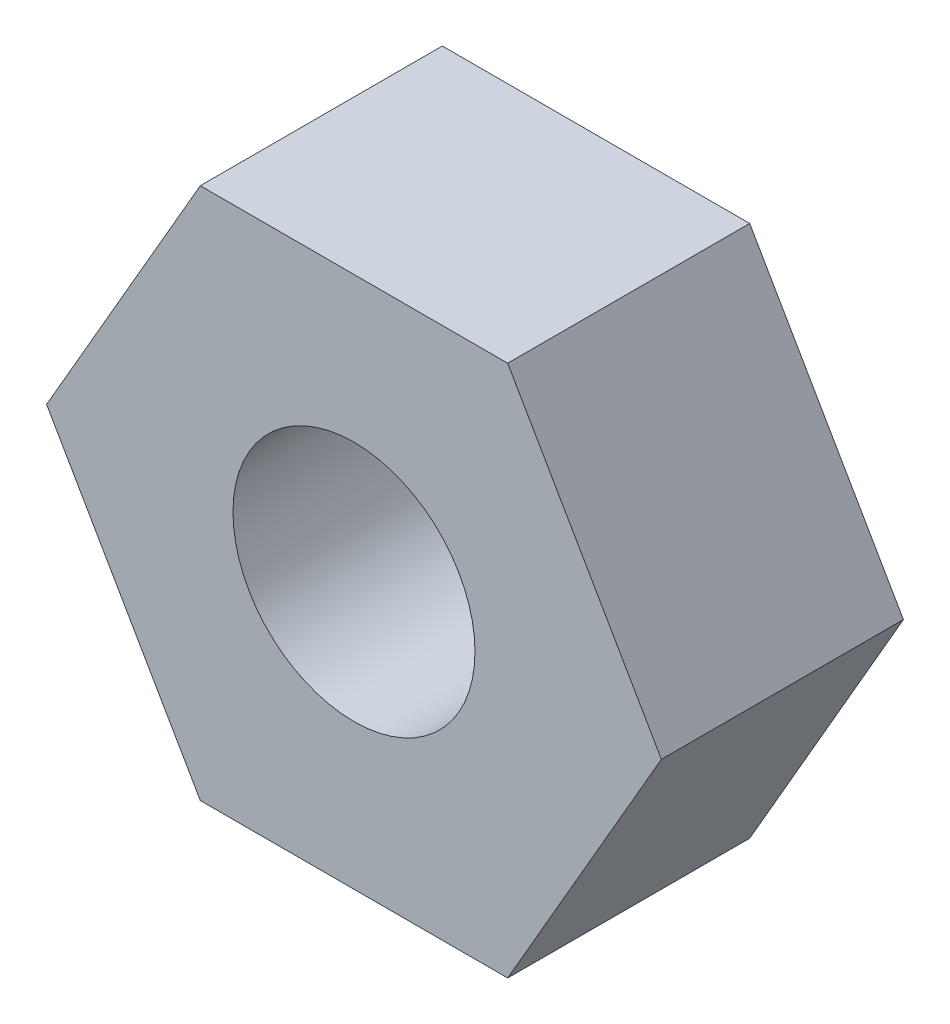
SolidWorks part; units mm, degrees
ref_plane "Front Plane" through (0, 0, 0) normal (0, 0, 1) x (1, 0, 0)
ref_plane "Top Plane" through (0, 0, 0) normal (0, 1, 0) x (1, 0, 0)
ref_plane "Right Plane" through (0, 0, 0) normal (1, 0, 0) x (0, 0, -1)
sketch "Esquisse1" plane through (0, 0, 0) normal (0, 0, 1) x (1, 0, 0)
  line L0 (-1.5877, 2.75) -> (1.5877, 2.75)
  line L1 (1.5877, 2.75) -> (3.1754, 0)
  line L2 (-3.1754, 0) -> (3.1754, 0) construction
  line L3 (1.5877, 2.75) -> (-1.5877, -2.75) construction
  line L4 (3.1754, 0) -> (1.5877, -2.75)
  line L5 (1.5877, -2.75) -> (-1.5877, -2.75)
  line L6 (-1.5877, -2.75) -> (-3.1754, 0)
  line L7 (-3.1754, 0) -> (-1.5877, 2.75)
  line L8 (-1.5877, 2.75) -> (1.5877, -2.75) construction
  circle A0 centre (0, 0) radius 1.25
  point P5 (0, 0)
  point P11 (0, 0)
  dimension "D1" = 2.5
  dimension "D2" = 5.5
extrude "Boss.-Extru.1" add sketch "Esquisse1" along normal blind 2.5
